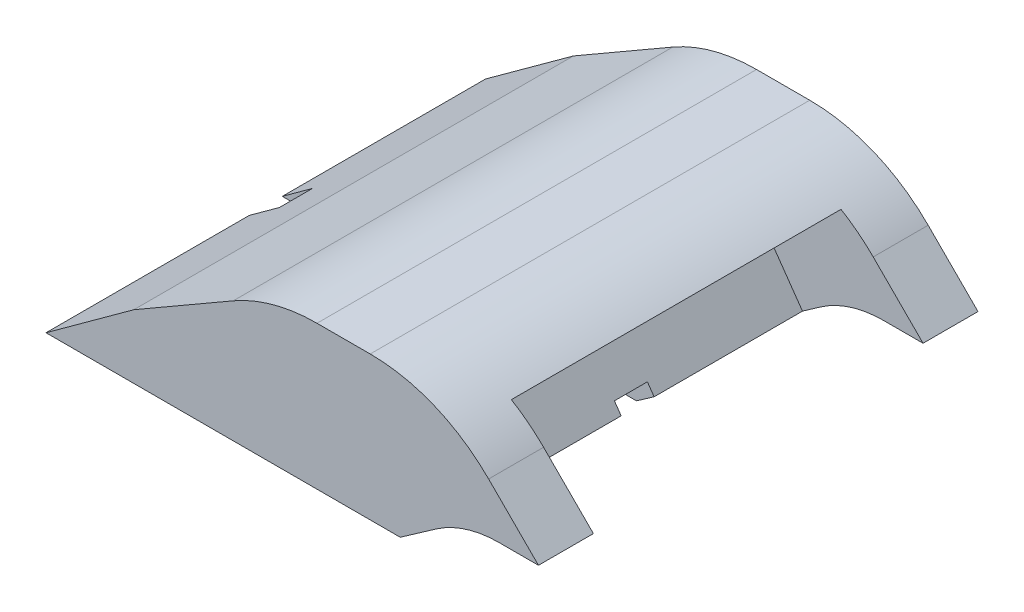
SolidWorks part; units mm, degrees
ref_plane "Front Plane" through (0, 0, 0) normal (0, 0, 1) x (1, 0, 0)
ref_plane "Top Plane" through (0, 0, 0) normal (0, 1, 0) x (1, 0, 0)
ref_plane "Right Plane" through (0, 0, 0) normal (1, 0, 0) x (0, 0, -1)
sketch "Sketch1" plane through (0, 0, 0) normal (0, 0, 1) x (1, 0, 0)
  line L0 (-21.1184, 5.5) -> (-17.1184, 8.4088)
  line L1 (-17.1184, 8.4088) -> (-10.8294, 12.0397)
  line L2 (-10.8294, 12.0397) -> (-3.2094, 12.0397)
  line L3 (-3.2094, 12.0397) -> (1.2906, 7.5397)
  line L4 (-21.1184, 5.5) -> (-4.9985, 5.5)
  line L5 (-4.9985, 5.5) -> (-3.3769, 6.6355)
  line L6 (-0.509, 7.5397) -> (1.2906, 7.5397)
  line L7 (3.0903, 7.5397) -> (-0.509, 7.5397) construction
  arc A1 (-3.3769, 6.6355) -> (-0.509, 7.5397) centre (-0.509, 2.5397) cw
  dimension "D1" = 4.5
  dimension "D2" = 150
  dimension "D3" = 4
  dimension "D4" = 135
  dimension "D5" = 7.62
extrude "Boss-Extrude1" add sketch "Sketch1" against normal up to surface (20 mm away)
fillet "Fillet1" radius 7.62 2 edges at (-10.8294, 12.0397, -10) (-3.2094, 12.0397, -10)
sketch "Sketch2" plane through (-4.2286, 6.0391, 0) normal (0.5736, -0.8192, 0) x (0.8192, 0.5736, 0)
  line L1 (0.0398, -2.5) -> (14.6814, -2.5)
  line L2 (0.0398, -2.5) -> (0.0398, -17.5)
  line L3 (0.0398, -17.5) -> (14.6814, -17.5)
  line L4 (14.6814, -2.5) -> (14.6814, -17.5)
  line L6 (1.0398, -10) -> (0.0398, -10) construction
  line L7 (1.0398, -20) -> (1.0398, 0) construction
  point P6 (0.0398, -10)
  dimension "D1" = 15
  dimension "D2" = 1
extrude "Cut-Extrude3" cut sketch "Sketch2" against normal blind 3 and the other way through all
sketch "Sketch3" plane through (0, 0, 0) normal (1, 0, 0) x (0, 0, -1)
  line L0 (20, 5.5) -> (0, 5.5) construction
  line L1 (9.25, 5.5) -> (10.75, 5.5)
  line L2 (9.25, 5.5) -> (9.25, 6.5)
  line L3 (9.25, 6.5) -> (10.75, 6.5)
  line L4 (10.75, 5.5) -> (10.75, 6.5)
  point P6 (10, 5.5)
  dimension "D1" = 1.5
  dimension "D2" = 1
extrude "Cut-Extrude4" cut sketch "Sketch3" against normal through all
